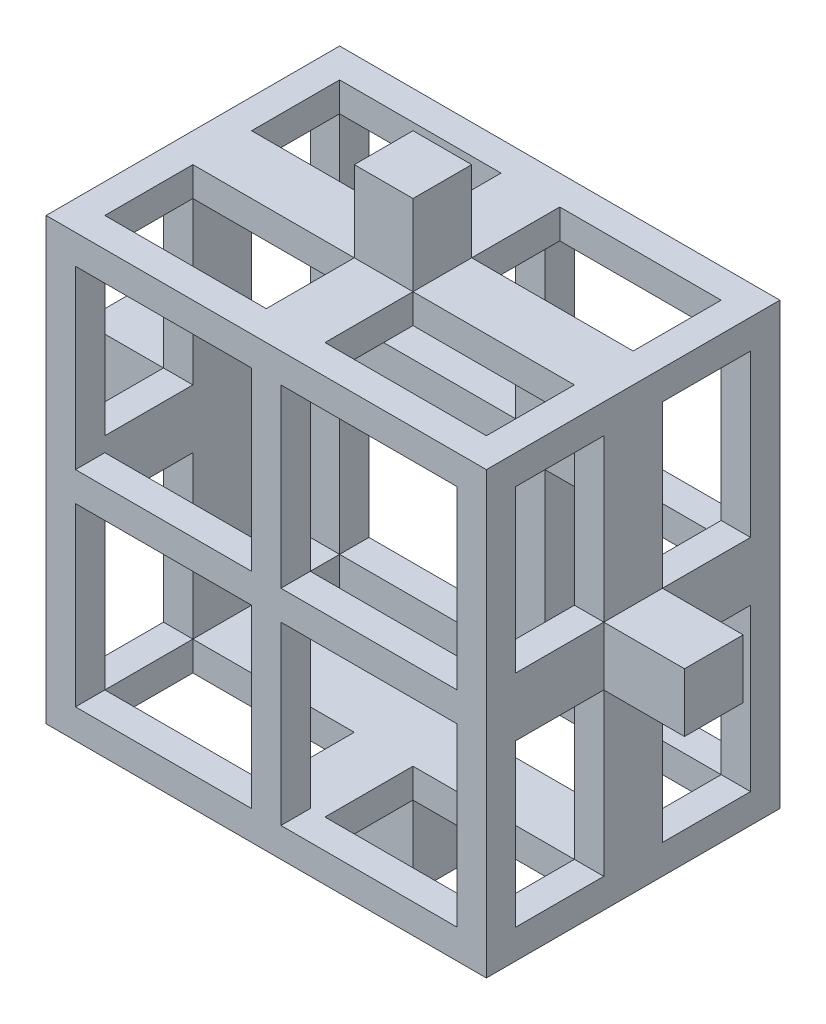
SolidWorks part; units mm, degrees
ref_plane "正面" through (0, 0, 0) normal (0, 0, 1) x (1, 0, 0)
ref_plane "平面" through (0, 0, 0) normal (0, 1, 0) x (1, 0, 0)
ref_plane "右側面" through (0, 0, 0) normal (1, 0, 0) x (0, 0, -1)
sketch "ｽｹｯﾁ1" plane through (0, 0, 0) normal (0, 0, 1) x (1, 0, 0)
  line L0 (-3.4179, 1.7541) -> (-6.1679, 1.7541)
  line L1 (-23.9179, 11.0041) -> (-3.4179, 11.0041) construction
  line L2 (-23.9179, 11.0041) -> (-23.9179, -9.4959) construction
  line L3 (-23.9179, -9.4959) -> (-3.4179, -9.4959) construction
  line L4 (-3.4179, 11.0041) -> (-3.4179, -9.4959) construction
  line L5 (-21.1679, 8.2541) -> (-6.1679, 8.2541)
  line L6 (-21.1679, 8.2541) -> (-21.1679, -6.7459)
  line L7 (-21.1679, -6.7459) -> (-6.1679, -6.7459)
  line L8 (-6.1679, 8.2541) -> (-6.1679, -6.7459)
  line L9 (-14.6679, 11.0041) -> (-12.6679, 11.0041)
  line L10 (-14.6679, 11.0041) -> (-14.6679, 8.2541)
  line L11 (-14.6679, 8.2541) -> (-12.6679, 8.2541)
  line L12 (-12.6679, 11.0041) -> (-12.6679, 8.2541)
  line L13 (-3.4179, 1.7541) -> (-3.4179, -0.2459)
  line L14 (-3.4179, -0.2459) -> (-6.1679, -0.2459)
  line L15 (-6.1679, 1.7541) -> (-6.1679, -0.2459)
  line L16 (-12.6679, -9.4959) -> (-12.6679, -6.7459)
  line L17 (-12.6679, -9.4959) -> (-14.6679, -9.4959)
  line L18 (-14.6679, -9.4959) -> (-14.6679, -6.7459)
  line L19 (-12.6679, -6.7459) -> (-14.6679, -6.7459)
  line L20 (-23.9179, -0.2459) -> (-21.1679, -0.2459)
  line L21 (-23.9179, -0.2459) -> (-23.9179, 1.7541)
  line L22 (-23.9179, 1.7541) -> (-21.1679, 1.7541)
  line L23 (-21.1679, -0.2459) -> (-21.1679, 1.7541)
  line L24 (-7.1679, 7.2541) -> (-13.1679, 7.2541)
  line L25 (-20.1679, 7.2541) -> (-14.1679, 7.2541)
  line L26 (-20.1679, 7.2541) -> (-20.1679, 1.2541)
  line L27 (-20.1679, 1.2541) -> (-14.1679, 1.2541)
  line L28 (-14.1679, 7.2541) -> (-14.1679, 1.2541)
  line L29 (-7.1679, 7.2541) -> (-7.1679, 1.2541)
  line L30 (-7.1679, 1.2541) -> (-13.1679, 1.2541)
  line L31 (-13.1679, 7.2541) -> (-13.1679, 1.2541)
  line L32 (-7.1679, -5.7459) -> (-7.1679, 0.2541)
  line L33 (-7.1679, -5.7459) -> (-13.1679, -5.7459)
  line L34 (-13.1679, -5.7459) -> (-13.1679, 0.2541)
  line L35 (-7.1679, 0.2541) -> (-13.1679, 0.2541)
  line L36 (-20.1679, -5.7459) -> (-14.1679, -5.7459)
  line L37 (-20.1679, -5.7459) -> (-20.1679, 0.2541)
  line L38 (-20.1679, 0.2541) -> (-14.1679, 0.2541)
  line L39 (-14.1679, -5.7459) -> (-14.1679, 0.2541)
  point P12 (-13.6679, 0.7541)
  point P28 (-13.6679, 0.7541)
  point P30 (-17.1679, 7.2541)
  point P46 (-13.6679, 0.7541)
  dimension "D1" = 20.5
  dimension "D2" = 20.5
  dimension "D3" = 15
  dimension "D4" = 15
  dimension "D5" = 2.75
  dimension "D6" = 2.75
  dimension "D7" = 2
  dimension "D8" = 6.5
  dimension "D9" = 7.5
  dimension "D10" = 7.5
  dimension "D12" = 6.5
  dimension "D13" = 6
  dimension "D14" = 6
  dimension "D15" = 1
  dimension "D16" = 1
  dimension "D11" = 4
  dimension "D17" = 4
extrude "ﾎﾞｽ - 押し出し1" add sketch "ｽｹｯﾁ1" along normal blind 10 contours L8 L5 L6 L7 L39 L36 L37 L38 L35 L32 L33 L34 L31 L24 L29 L30 L25 L28 L27 L26 | L12 L9 L10 L5 | L22 L21 L20 L6 | L14 L15 L0 L13 | L16 L19 L18 L17
sketch "ｽｹｯﾁ2" plane through (0, 11.0041, 0) normal (0, 1, 0) x (1, 0, 0)
  line L0 (-12.6679, -10) -> (-12.6679, 0) construction
  line L1 (-14.6679, 0) -> (-12.6679, 0)
  line L2 (-14.6679, 0) -> (-14.6679, -4)
  line L3 (-14.6679, -4) -> (-12.6679, -4)
  line L4 (-12.6679, 0) -> (-12.6679, -4)
  line L6 (-14.6679, -10) -> (-12.6679, -10)
  line L7 (-14.6679, -10) -> (-14.6679, -6)
  line L8 (-14.6679, -6) -> (-12.6679, -6)
  line L9 (-12.6679, -10) -> (-12.6679, -6)
  dimension "D1" = 4
  dimension "D2" = 4
extrude "ｶｯﾄ - 押し出し1" cut sketch "ｽｹｯﾁ2" against normal blind 2.75
sketch "ｽｹｯﾁ3" plane through (-3.4179, 0, 0) normal (1, 0, 0) x (0, 0, -1)
  line L0 (-10, -0.2459) -> (0, -0.2459) construction
  line L1 (-10, 1.7541) -> (-6, 1.7541)
  line L2 (-10, 1.7541) -> (-10, -0.2459)
  line L3 (-10, -0.2459) -> (-6, -0.2459)
  line L4 (-6, 1.7541) -> (-6, -0.2459)
  line L5 (-10, -0.2459) -> (0, -0.2459) construction
  line L6 (0, 1.7541) -> (-4, 1.7541)
  line L7 (0, 1.7541) -> (0, -0.2459)
  line L8 (0, -0.2459) -> (-4, -0.2459)
  line L9 (-4, 1.7541) -> (-4, -0.2459)
  dimension "D1" = 4
  dimension "D2" = 4
extrude "ｶｯﾄ - 押し出し2" cut sketch "ｽｹｯﾁ3" against normal blind 2.75
sketch "ｽｹｯﾁ4" plane through (0, -9.4959, 0) normal (0, -1, 0) x (1, 0, 0)
  line L0 (-12.6679, 10) -> (-12.6679, 0) construction
  line L1 (-14.6679, 10) -> (-12.6679, 10)
  line L2 (-14.6679, 10) -> (-14.6679, 6)
  line L3 (-14.6679, 6) -> (-12.6679, 6)
  line L4 (-12.6679, 10) -> (-12.6679, 6)
  line L6 (-14.6679, 0) -> (-12.6679, 0)
  line L7 (-14.6679, 0) -> (-14.6679, 4)
  line L8 (-14.6679, 4) -> (-12.6679, 4)
  line L9 (-12.6679, 0) -> (-12.6679, 4)
  dimension "D1" = 4
  dimension "D2" = 4
extrude "ｶｯﾄ - 押し出し3" cut sketch "ｽｹｯﾁ4" against normal blind 2.75
sketch "ｽｹｯﾁ5" plane through (-23.9179, 0, 0) normal (-1, 0, 0) x (0, 0, 1)
  line L0 (10, -0.2459) -> (0, -0.2459) construction
  line L1 (0, 1.7541) -> (4, 1.7541)
  line L2 (0, 1.7541) -> (0, -0.2459)
  line L3 (0, -0.2459) -> (4, -0.2459)
  line L4 (4, 1.7541) -> (4, -0.2459)
  line L6 (10, 1.7541) -> (6, 1.7541)
  line L7 (10, 1.7541) -> (10, -0.2459)
  line L8 (10, -0.2459) -> (6, -0.2459)
  line L9 (6, 1.7541) -> (6, -0.2459)
  dimension "D1" = 4
  dimension "D2" = 4
extrude "ｶｯﾄ - 押し出し4" cut sketch "ｽｹｯﾁ5" against normal blind 2.75
sketch "ｽｹｯﾁ6" plane through (0, 8.2541, 0) normal (0, 1, 0) x (1, 0, 0)
  line L0 (-21.1679, 0) -> (-6.1679, 0) construction
  line L1 (-20.1679, -1) -> (-14.6679, -1)
  line L2 (-20.1679, -1) -> (-20.1679, -4)
  line L3 (-20.1679, -4) -> (-14.6679, -4)
  line L4 (-14.6679, -1) -> (-14.6679, -4)
  line L5 (-21.1679, -10) -> (-21.1679, 0) construction
  line L6 (-12.6679, -1) -> (-12.6679, -4)
  line L7 (-12.6679, -1) -> (-7.1679, -1)
  line L8 (-7.1679, -1) -> (-7.1679, -4)
  line L9 (-12.6679, -4) -> (-7.1679, -4)
  line L10 (-20.1679, -6) -> (-20.1679, -9)
  line L11 (-20.1679, -6) -> (-14.6679, -6)
  line L12 (-14.6679, -6) -> (-14.6679, -9)
  line L13 (-20.1679, -9) -> (-14.6679, -9)
  line L14 (-12.6679, -6) -> (-12.6679, -9)
  line L15 (-12.6679, -9) -> (-7.1679, -9)
  line L16 (-7.1679, -6) -> (-7.1679, -9)
  line L17 (-12.6679, -6) -> (-7.1679, -6)
  dimension "D1" = 4
  dimension "D2" = 1
  dimension "D3" = 1
  dimension "D4" = 2
  dimension "D5" = 2
  dimension "D6" = 2
extrude "ｶｯﾄ - 押し出し5" cut sketch "ｽｹｯﾁ6" against normal through all
sketch "ｽｹｯﾁ7" plane through (-6.1679, 0, 0) normal (1, 0, 0) x (0, 0, -1)
  line L1 (-6, 1.7541) -> (-9, 1.7541)
  line L2 (-6, 1.7541) -> (-6, 7.2541)
  line L3 (-6, 7.2541) -> (-9, 7.2541)
  line L4 (-9, 1.7541) -> (-9, 7.2541)
  line L5 (-1, 1.7541) -> (-1, 7.2541)
  line L6 (-1, 1.7541) -> (-4, 1.7541)
  line L7 (-4, 1.7541) -> (-4, 7.2541)
  line L8 (-1, 7.2541) -> (-4, 7.2541)
  line L9 (-6, -5.7459) -> (-6, -0.2459)
  line L10 (-6, -5.7459) -> (-9, -5.7459)
  line L11 (-9, -5.7459) -> (-9, -0.2459)
  line L12 (-6, -0.2459) -> (-9, -0.2459)
  line L13 (-1, -5.7459) -> (-1, -0.2459)
  line L14 (-1, -0.2459) -> (-4, -0.2459)
  line L15 (-4, -5.7459) -> (-4, -0.2459)
  line L16 (-1, -5.7459) -> (-4, -5.7459)
  dimension "D1" = 3
  dimension "D2" = 5.5
  dimension "D3" = 2
  dimension "D4" = 2
extrude "ｶｯﾄ - 押し出し6" cut sketch "ｽｹｯﾁ7" against normal through all
sketch "ｽｹｯﾁ8" plane through (-14.1679, 0, 0) normal (-1, 0, 0) x (0, 0, 1)
  line L1 (1, 7.2541) -> (9, 7.2541)
  line L2 (1, 7.2541) -> (1, -5.7459)
  line L3 (1, -5.7459) -> (9, -5.7459)
  line L4 (9, 7.2541) -> (9, -5.7459)
extrude "ｶｯﾄ - 押し出し7" cut sketch "ｽｹｯﾁ8" along normal blind 6 and the other way blind 0.75
sketch "ｽｹｯﾁ9" plane through (-13.1679, 0, 0) normal (1, 0, 0) x (0, 0, -1)
  line L1 (-9, 7.2541) -> (-1, 7.2541)
  line L2 (-9, 7.2541) -> (-9, -5.7459)
  line L3 (-9, -5.7459) -> (-1, -5.7459)
  line L4 (-1, 7.2541) -> (-1, -5.7459)
extrude "ｶｯﾄ - 押し出し8" cut sketch "ｽｹｯﾁ9" along normal blind 6
sketch "ｽｹｯﾁ10" plane through (-13.1679, 0, 0) normal (1, 0, 0) x (0, 0, -1)
  line L1 (-9, 7.2541) -> (-1, 7.2541)
  line L2 (-9, 7.2541) -> (-9, -5.7459)
  line L3 (-9, -5.7459) -> (-1, -5.7459)
  line L4 (-1, 7.2541) -> (-1, -5.7459)
extrude "ｶｯﾄ - 押し出し9" cut sketch "ｽｹｯﾁ10" against normal blind 6
equation "\"2..75mm\"=10"
